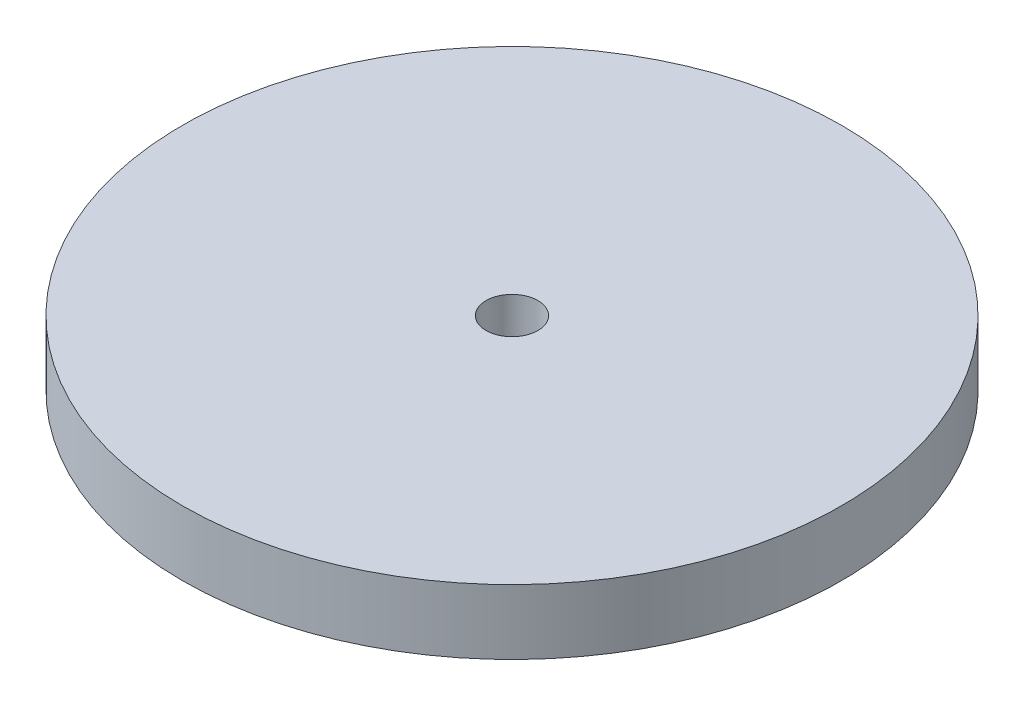
SolidWorks part; units mm, degrees
ref_plane "Front Plane" through (0, 0, 0) normal (0, 0, 1) x (1, 0, 0)
ref_plane "Top Plane" through (0, 0, 0) normal (0, 1, 0) x (1, 0, 0)
ref_plane "Right Plane" through (0, 0, 0) normal (1, 0, 0) x (0, 0, -1)
sketch "Sketch1" plane through (0, 0, 0) normal (0, 1, 0) x (1, 0, 0)
  circle A0 centre (0, 0) radius 50.8
extrude "Boss-Extrude1" add sketch "Sketch1" along normal blind 10
sketch "Sketch2" plane through (0, 10, 0) normal (0, 1, 0) x (1, 0, 0)
  circle A0 centre (0, 0) radius 4
  dimension "D1" = 8
extrude "Cut-Extrude1" cut sketch "Sketch2" against normal through all
